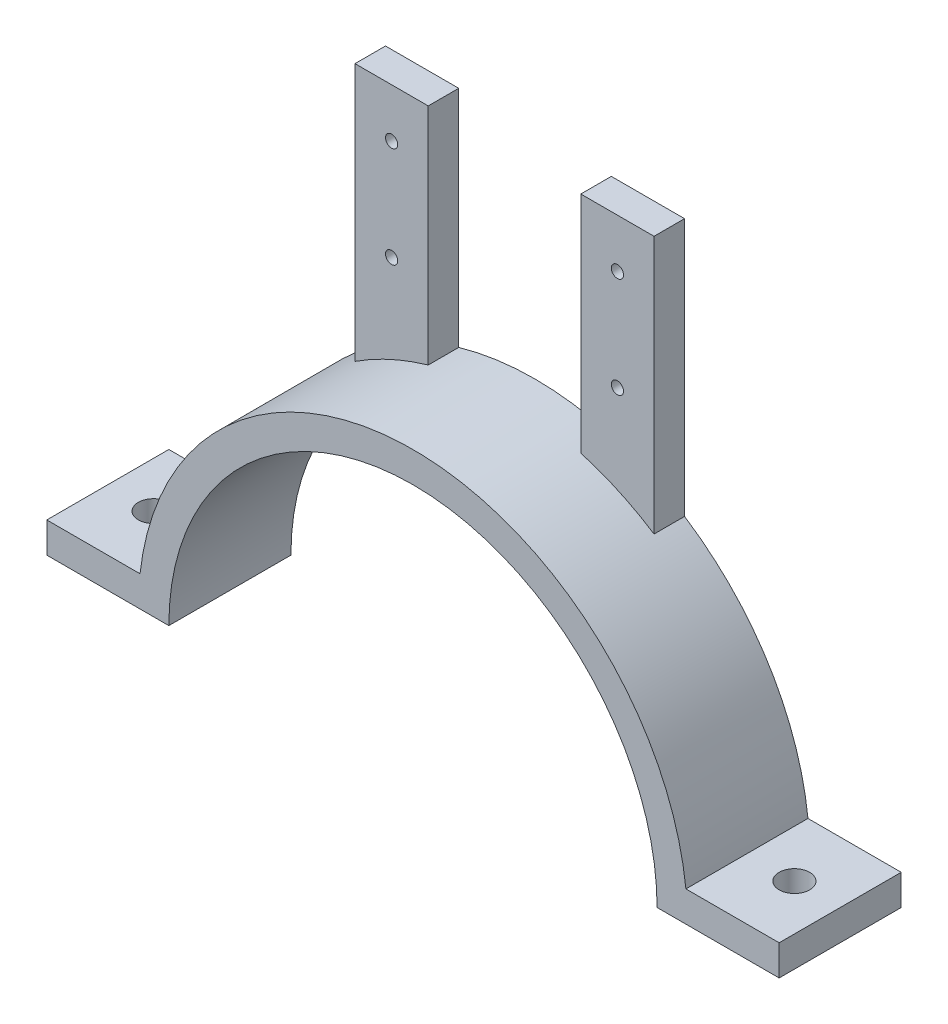
SolidWorks part; units mm, degrees
ref_plane "Front Plane" through (0, 0, 0) normal (0, 0, 1) x (1, 0, 0)
ref_plane "Top Plane" through (0, 0, 0) normal (0, 1, 0) x (1, 0, 0)
ref_plane "Right Plane" through (0, 0, 0) normal (1, 0, 0) x (0, 0, -1)
sketch "Sketch1" plane through (0, 0, 0) normal (0, 0, 1) x (1, 0, 0)
  line L0 (-45, 0) -> (-40, 0)
  line L1 (40, 0) -> (45, 0)
  line L2 (-45, 0) -> (-60, 0)
  line L3 (-60, 0) -> (-60, 5)
  line L4 (-60, 5) -> (-44.7214, 5)
  line L5 (60, 5) -> (60, 0)
  line L6 (60, 0) -> (45, 0)
  line L7 (44.7214, 5) -> (60, 5)
  arc A0 (40, 0) -> (-40, 0) centre (0, 0) ccw
  arc A1 (44.7214, 5) -> (-44.7214, 5) centre (0, 0) ccw
  dimension "D1" = 40
  dimension "D3" = 45
  dimension "D2" = 15
  dimension "D4" = 15
  dimension "D5" = 5
extrude "Boss-Extrude1" add sketch "Sketch1" along normal blind 20
sketch3d "3DSketch3"
  line L1 (-24.5, 37.7459, 0) -> (-24.5, 80, 0)
  line L2 (-24.5, 80, 0) -> (-12.5, 80, 0)
  line L3 (-12.5, 80, 0) -> (-12.5, 43.229, 0)
  line L4 (12.5, 43.229, 0) -> (12.5, 80, 0)
  line L5 (12.5, 80, 0) -> (24.4998, 80, 0)
  line L6 (24.4998, 80, 0) -> (24.4998, 37.746, 0)
  arc A1 (44.7214, 5, 0) -> (-44.7214, 5, 0) centre (0, 0, 0) ccw construction
  arc A2 (24.4998, 37.746, 0) -> (12.5, 43.229, 0) centre (0, 0, 0) ccw
  arc A3 (-12.5, 43.229, 0) -> (-24.5, 37.7459, 0) centre (0, 0, 0) ccw
  circle A4 centre (-18.5, 72, 0) radius 1
  circle A5 centre (18.5, 72, 0) radius 1
  circle A6 centre (-18.5, 55.5, 0) radius 1
  circle A7 centre (18.5, 55.5, 0) radius 1
  point P1 (0, 0, 45)
  point P12 (0, 0, 45)
  point P13 (0, 0, 45)
  point P17 (-18.5, 72, 1)
  point P20 (18.5, 72, 1)
  point P23 (-18.5, 55.5, 1)
  point P26 (18.5, 55.5, 1)
  dimension "D2" = 12.5
  dimension "D6" = 80
  dimension "D3" = 2
  dimension "D5" = 2
  dimension "D8" = 2
  dimension "D9" = 2
  dimension "D1" = 7.5
  dimension "D4" = 12.5
  dimension "D7" = 80
  dimension "D10" = 8
  dimension "D11" = 8
  dimension "D12" = 6
  dimension "D13" = 6
  dimension "D14" = 6
  dimension "D15" = 16.5
  dimension "D16" = 6
  dimension "D17" = 16.5
extrude "Boss-Extrude2" add sketch "3DSketch3" along a picked direction on the side against the normal blind 5
sketch "Sketch2" plane through (0, 0, 0) normal (0, 0, -1) x (-1, 0, 0)
  line L1 (-16.19, 55.5) -> (-17.345, 57.5005)
  line L2 (-17.345, 57.5005) -> (-19.655, 57.5005)
  line L3 (-19.655, 57.5005) -> (-20.81, 55.5)
  line L4 (-20.81, 55.5) -> (-19.655, 53.4995)
  line L5 (-19.655, 53.4995) -> (-17.345, 53.4995)
  line L6 (-17.345, 53.4995) -> (-16.19, 55.5)
  line L7 (-16.19, 72) -> (-17.345, 74.0005)
  line L8 (-17.345, 74.0005) -> (-19.655, 74.0005)
  line L9 (-19.655, 74.0005) -> (-20.81, 72)
  line L10 (-20.81, 72) -> (-19.655, 69.9995)
  line L11 (-19.655, 69.9995) -> (-17.345, 69.9995)
  line L12 (-17.345, 69.9995) -> (-16.19, 72)
  line L13 (20.81, 72) -> (19.655, 74.0005)
  line L14 (19.655, 74.0005) -> (17.345, 74.0005)
  line L15 (17.345, 74.0005) -> (16.19, 72)
  line L16 (16.19, 72) -> (17.345, 69.9995)
  line L17 (17.345, 69.9995) -> (19.655, 69.9995)
  line L18 (19.655, 69.9995) -> (20.81, 72)
  line L19 (20.81, 55.5) -> (19.655, 57.5005)
  line L20 (19.655, 57.5005) -> (17.345, 57.5005)
  line L21 (17.345, 57.5005) -> (16.19, 55.5)
  line L22 (16.19, 55.5) -> (17.345, 53.4995)
  line L23 (17.345, 53.4995) -> (19.655, 53.4995)
  line L24 (19.655, 53.4995) -> (20.81, 55.5)
  circle A0 centre (-18.5, 55.5) radius 2.0005 construction
  circle A1 centre (-18.5, 72) radius 2.0005 construction
  circle A2 centre (18.5, 72) radius 2.0005 construction
  circle A3 centre (18.5, 55.5) radius 2.0005 construction
  dimension "D1" = 2.31
  dimension "D2" = 2.31
  dimension "D3" = 2.31
  dimension "D4" = 2.31
extrude "Cut-Extrude1" cut sketch "Sketch2" against normal blind 2.5
sketch "Sketch3" plane through (0, 5, 0) normal (0, 1, 0) x (1, 0, 0)
  line L0 (-44.7214, 0) -> (-60, 0) construction
  line L1 (60, 0) -> (44.7214, 0) construction
  line L2 (-60, -20) -> (-60, 0) construction
  line L4 (60, -20) -> (60, 0) construction
  circle A0 centre (-52.5, -10) radius 2.5
  circle A1 centre (52.5, -10) radius 2.5
  dimension "D1" = 5
  dimension "D2" = 5
  dimension "D3" = 10
  dimension "D4" = 10
  dimension "D5" = 7.5
  dimension "D6" = 7.5
extrude "Cut-Extrude2" cut sketch "Sketch3" against normal through all
